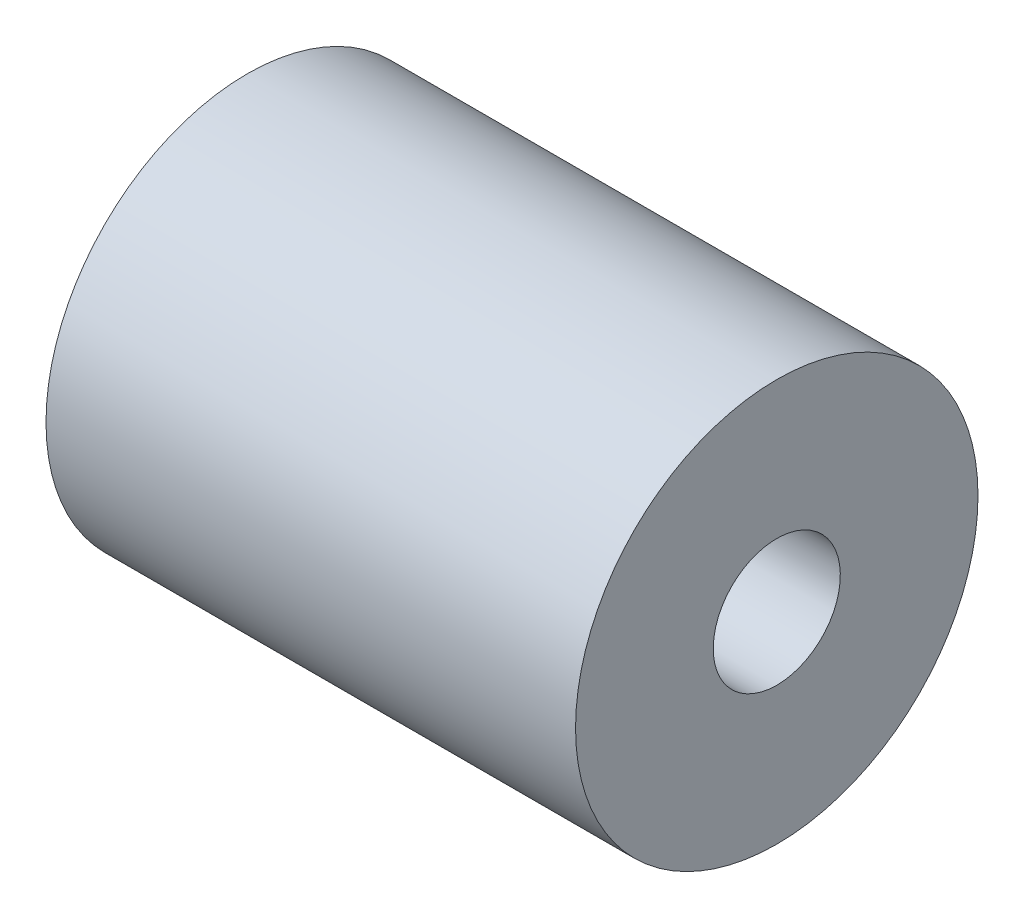
SolidWorks part; units mm, degrees
ref_plane "Front Plane" through (0, 0, 0) normal (0, 0, 1) x (1, 0, 0)
ref_plane "Top Plane" through (0, 0, 0) normal (0, 1, 0) x (1, 0, 0)
ref_plane "Right Plane" through (0, 0, 0) normal (1, 0, 0) x (0, 0, -1)
sketch "Sketch1" plane through (0, 0, 0) normal (0, 0, 1) x (1, 0, 0)
  line L0 (-12.5, 0) -> (12.5, 0) construction
  line L2 (12.5, 3) -> (12.5, 9.5)
  line L3 (12.5, 9.5) -> (-12.5, 9.5)
  line L4 (-12.5, 9.5) -> (-12.5, 4)
  line L5 (12.5, 3) -> (1.4114, 3)
  line L6 (1.4114, 3) -> (1.4114, 4)
  line L7 (1.4114, 4) -> (-12.5, 4)
  point P4 (0, 0)
  dimension "D1" = 25
  dimension "D2" = 6
  dimension "D3" = 8
  dimension "D4" = 19
  dimension "D5" = 25
  dimension "D6" = 11.0886
revolve "Revolve1" add sketch "Sketch1" angle 360 about L0
